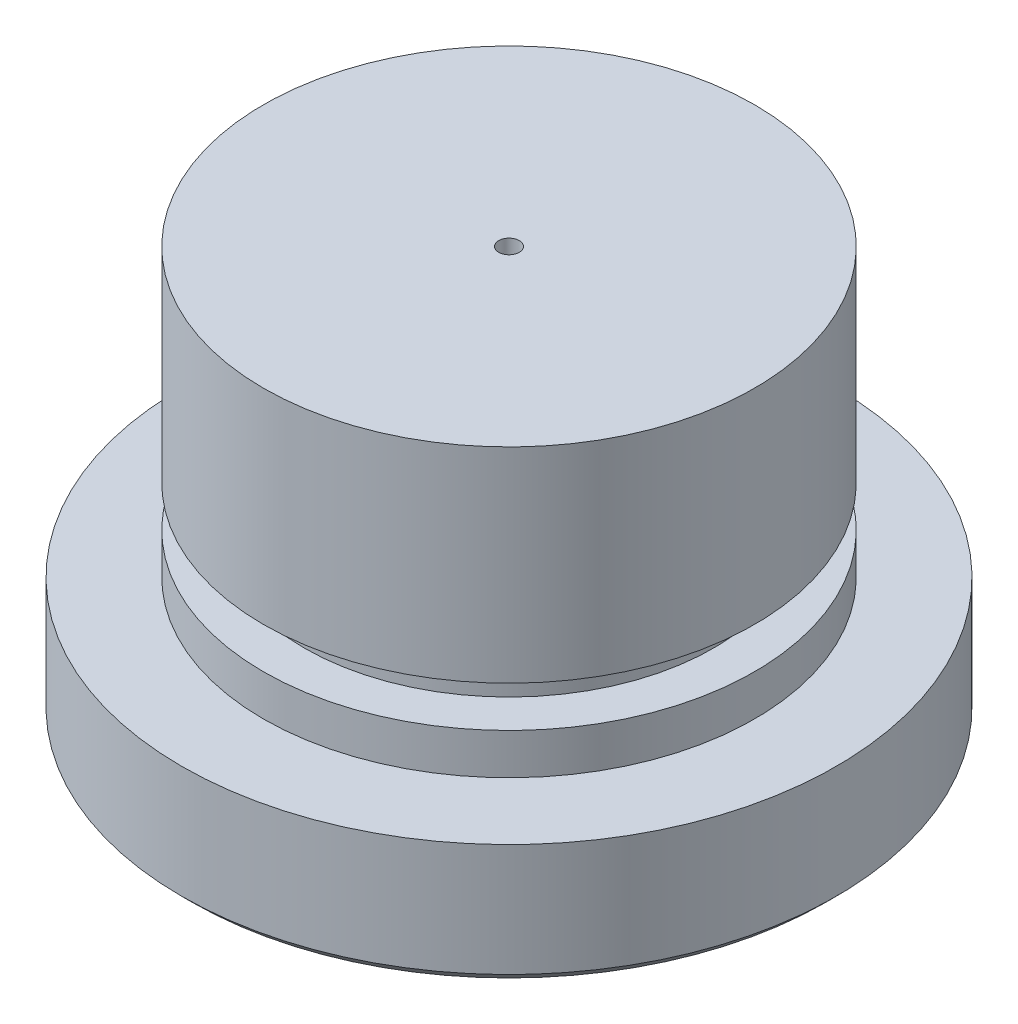
SolidWorks part; units mm, degrees
ref_plane "Front Plane" through (0, 0, 0) normal (0, 0, 1) x (1, 0, 0)
ref_plane "Top Plane" through (0, 0, 0) normal (0, 1, 0) x (1, 0, 0)
ref_plane "Right Plane" through (0, 0, 0) normal (1, 0, 0) x (0, 0, -1)
sketch "Sketch1" plane through (0, 0, 0) normal (0, 1, 0) x (1, 0, 0)
  circle A0 centre (0, 0) radius 12.7
  dimension "D1" = 25.4
extrude "Boss-Extrude1" add sketch "Sketch1" along normal blind 15.875
sketch "Sketch2" plane through (0, 15.875, 0) normal (0, 1, 0) x (1, 0, 0)
  circle A0 centre (0, 0) radius 9.525
  circle A1 centre (0, 0) radius 12.7
  circle M1 centre (0, 0) radius 12.7
  dimension "D1" = 19.05
extrude "Cut-Extrude1" cut sketch "Sketch2" against normal blind 11.1125 contours A0 M1
sketch "Sketch3" plane through (0, 0, 0) normal (0, -1, 0) x (1, 0, 0)
  circle A0 centre (0, 0) radius 0.3969
  dimension "D1" = 0.7937
extrude "Cut-Extrude2" cut sketch "Sketch3" against normal through all
chamfer "Chamfer1" distance 0.3969 angle 45 1 edges at (0, 0, 12.7)
ref_plane "Plane1" through (0, 6.35, 0) normal (0, 1, 0) x (1, 0, 0)
sketch "Sketch4" plane through (0, 6.35, 0) normal (0, 1, 0) x (1, 0, 0)
  circle A0 centre (0, 0) radius 9.525
  circle A1 centre (0, 0) radius 7.9375
  dimension "D1" = 19.05
  dimension "D2" = 1.5875
extrude "Cut-Extrude3" cut sketch "Sketch4" along normal blind 1.5875 contours A0 A1
